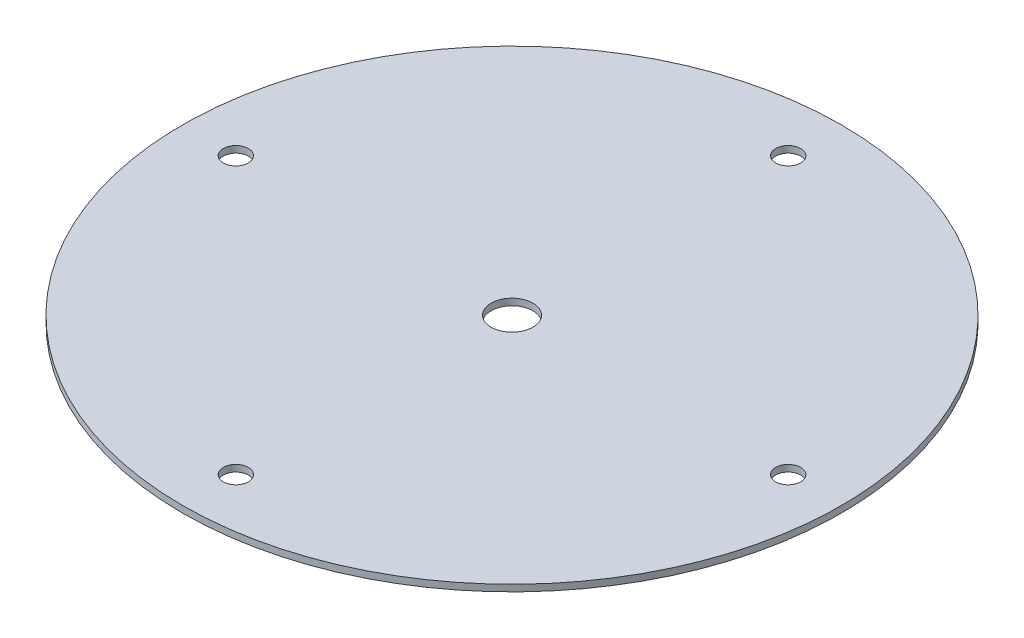
SolidWorks part; units mm, degrees
ref_plane "Front Plane" through (0, 0, 0) normal (0, 0, 1) x (1, 0, 0)
ref_plane "Top Plane" through (0, 0, 0) normal (0, 1, 0) x (1, 0, 0)
ref_plane "Right Plane" through (0, 0, 0) normal (1, 0, 0) x (0, 0, -1)
sketch "Sketch1" plane through (0, 0, 0) normal (0, 1, 0) x (1, 0, 0)
  line L0 (0, 0) -> (0, 66.2) construction
  circle A0 centre (0, 0) radius 79
  circle A1 centre (0, 66.2) radius 3
  circle A2 centre (66.2, 0) radius 3
  circle A3 centre (0, -66.2) radius 3
  circle A4 centre (-66.2, 0) radius 3
  circle A5 centre (0, 0) radius 5
  dimension "D1" = 158
  dimension "D2" = 6
  dimension "D6" = 10
  dimension "D3" = 66.2
  dimension "D5" = 66.2
  dimension "D4" = 4
extrude "Boss-Extrude1" add sketch "Sketch1" along normal blind 1.5875
